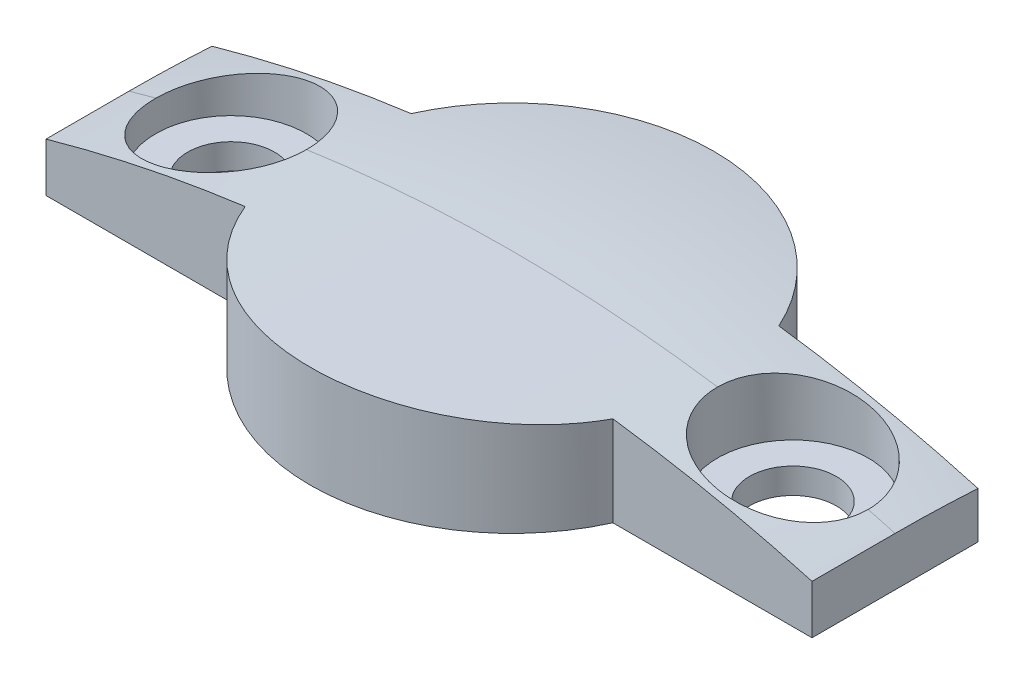
SolidWorks part; units mm, degrees
ref_plane "Alzado" through (0, 0, 0) normal (0, 0, 1) x (1, 0, 0)
ref_plane "Planta" through (0, 0, 0) normal (0, 1, 0) x (1, 0, 0)
ref_plane "Vista lateral" through (0, 0, 0) normal (1, 0, 0) x (0, 0, -1)
sketch "Croquis1" plane through (0, 0, 0) normal (0, 1, 0) x (1, 0, 0)
  line L0 (-7.2005, 3.25) -> (-15, 3.25)
  line L1 (15, -3.25) -> (7.2005, -3.25)
  line L2 (15, -3.25) -> (15, 3.25)
  line L3 (15, 3.25) -> (7.2005, 3.25)
  line L4 (-15, -3.25) -> (-15, 3.25)
  line L5 (15, -3.25) -> (-15, 3.25) construction
  line L6 (15, 3.25) -> (-15, -3.25) construction
  line L7 (-7.2005, -3.25) -> (-15, -3.25)
  arc A0 (-7.2005, -3.25) -> (7.2005, -3.25) centre (0, 0) ccw
  arc A1 (7.2005, 3.25) -> (-7.2005, 3.25) centre (0, 0) ccw
  point P0 (0, 0)
  dimension "D3" = 7.9
  dimension "D1" = 6.5
  dimension "D2" = 30
extrude "Saliente-Extruir1" add sketch "Croquis1" along normal blind 4
sketch "Croquis2" plane through (0, 4, 0) normal (0, 1, 0) x (1, 0, 0)
  line L1 (-11, 0) -> (11, 0) construction
  circle A0 centre (-11, 0) radius 1.7
  circle A1 centre (11, 0) radius 1.7
  point P0 (0, 0)
  dimension "D2" = 3.4
  dimension "D1" = 22
extrude "Cortar-Extruir1" cut sketch "Croquis2" against normal blind 4
sketch "Croquis3" plane through (0, 4, 0) normal (0, 1, 0) x (1, 0, 0)
  circle A0 centre (-11, 0) radius 2.95
  circle A1 centre (11, 0) radius 2.95
  dimension "D1" = 5.9
extrude "Cortar-Extruir2" cut sketch "Croquis3" against normal blind 3
sketch "Croquis4" plane through (0, 0, 0) normal (1, 0, 0) x (0, 0, -1)
  line L0 (0, 4) -> (-10, 4)
  line L1 (-3.25, 4) -> (3.25, 4) construction
  line L2 (-10, 4) -> (-10, 7)
  line L3 (-10, 7) -> (10, 7)
  line L4 (10, 7) -> (10, 3.0833)
  line L5 (-21.726, -51) -> (33.404, -51) construction
  arc A0 (0, 4) -> (10, 3.0833) centre (0, -51) cw
  point P5 (0, 7)
  dimension "D3" = 55
  dimension "D1" = 20
  dimension "D2" = 3
  dimension "D4" = 51
revolve "Cortar-Revolución1" cut sketch "Croquis4" angle 360 about L5
